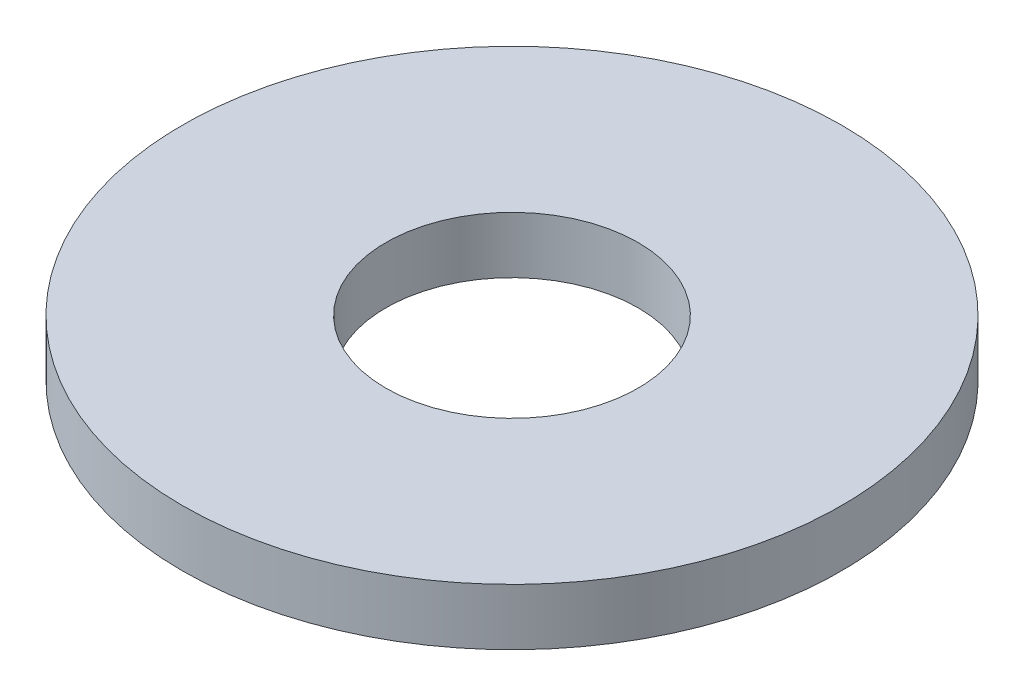
SolidWorks part; units mm, degrees
ref_plane "Plan de face" through (0, 0, 0) normal (0, 0, 1) x (1, 0, 0)
ref_plane "Plan de dessus" through (0, 0, 0) normal (0, 1, 0) x (1, 0, 0)
ref_plane "Plan de droite" through (0, 0, 0) normal (1, 0, 0) x (0, 0, -1)
sketch "Esquisse1" plane through (0, 0, 0) normal (0, 1, 0) x (1, 0, 0)
  circle A0 centre (0, 0) radius 9.3218
  circle A1 centre (0, 0) radius 3.5687
  dimension "Diam ext" = 18.6436
  dimension "Diam int" = 7.1374
extrude "Boss.-Extru.1" add sketch "Esquisse1" along normal blind 1.6002
